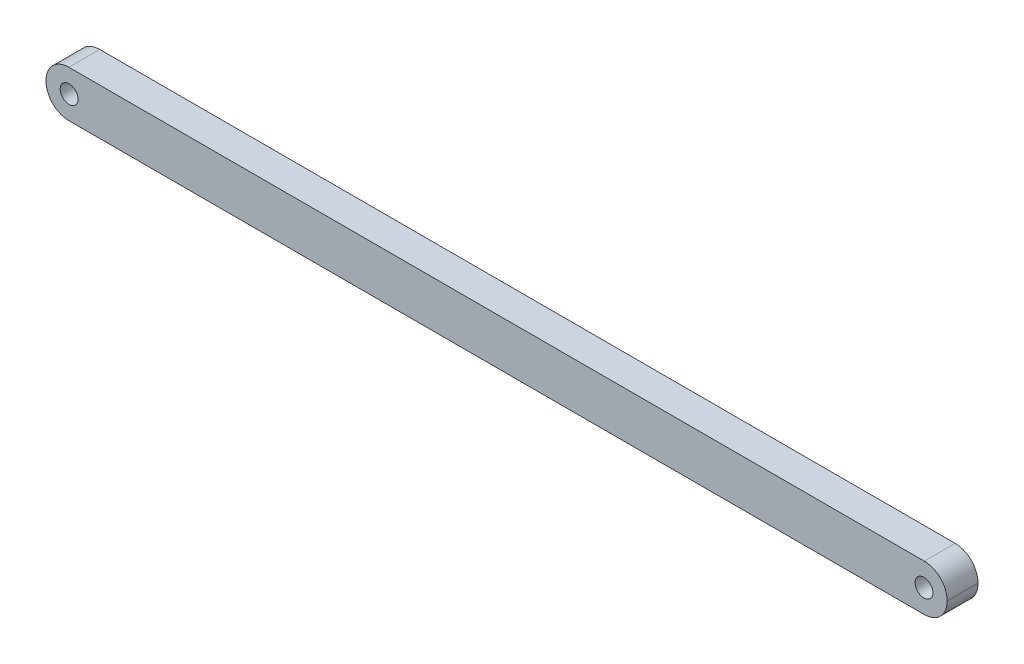
SolidWorks part; units mm, degrees
ref_plane "Front Plane" through (0, 0, 0) normal (0, 0, 1) x (1, 0, 0)
ref_plane "Top Plane" through (0, 0, 0) normal (0, 1, 0) x (1, 0, 0)
ref_plane "Right Plane" through (0, 0, 0) normal (1, 0, 0) x (0, 0, -1)
sketch "Sketch1" plane through (0, 0, 0) normal (0, 0, 1) x (1, 0, 0)
  line L0 (0, -7.5) -> (0, -1.9689)
  line L1 (-138.65, -7.5) -> (138.65, -7.5)
  line L2 (-146.05, -0.1) -> (-146.05, 0.1)
  line L3 (-138.65, 7.5) -> (138.65, 7.5)
  line L4 (146.05, -0.1) -> (146.05, 0.1)
  line L5 (-146.05, -7.5) -> (146.05, 7.5) construction
  line L6 (-146.05, 7.5) -> (146.05, -7.5) construction
  circle A0 centre (-138.55, 0) radius 2.9
  arc A1 (138.65, -7.5) -> (146.05, -0.1) centre (138.65, -0.1) ccw
  arc A2 (138.65, 7.5) -> (146.05, 0.1) centre (138.65, 0.1) cw
  arc A3 (-138.65, -7.5) -> (-146.05, -0.1) centre (-138.65, -0.1) cw
  arc A4 (-146.05, 0.1) -> (-138.65, 7.5) centre (-138.65, 0.1) cw
  circle A5 centre (138.55, 0) radius 2.9
  point P0 (0, 0)
  dimension "D5" = 5.8
  dimension "D6" = 7.4
  dimension "D1" = 15
  dimension "D2" = 292.1
  dimension "D3" = 7.5
  dimension "D4" = 7.5
extrude "Boss-Extrude1" add sketch "Sketch1" along normal blind 10
